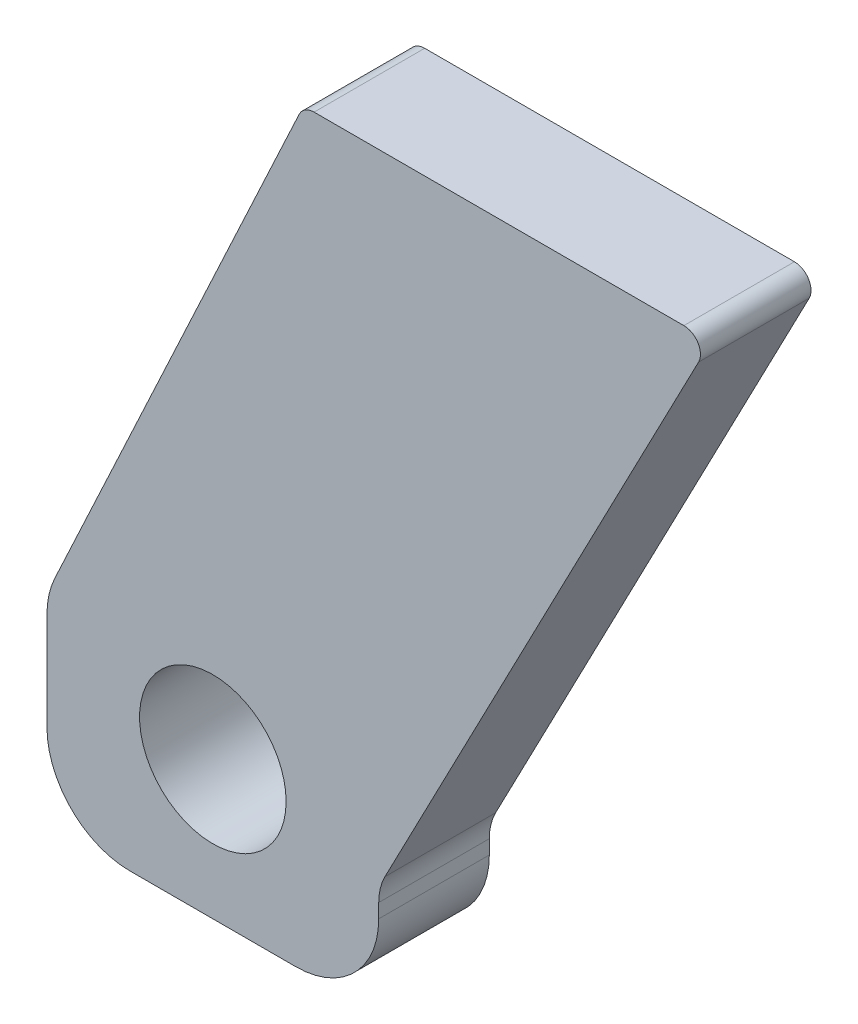
SolidWorks part; units mm, degrees
ref_plane "Plane1" through (0, 0, 0) normal (0, 0, 1) x (1, 0, 0)
ref_plane "Plane2" through (0, 0, 0) normal (0, 1, 0) x (1, 0, 0)
ref_plane "Plane3" through (0, 0, 0) normal (1, 0, 0) x (0, 0, -1)
sketch "Sketch1" plane through (0, 0, 0) normal (0, 0, 1) x (1, 0, 0)
  line L0 (13.25, 0) -> (-30, 0) construction
  line L1 (30, -7.447) -> (30, -10)
  line L3 (18.3088, 110.5) -> (85.1816, 110.5)
  line L4 (0, 0) -> (-65, 0) construction
  line L6 (-30, 7.6746) -> (-30, -10)
  line L7 (-28.5946, 14.0139) -> (15.5899, 108.7679)
  line L9 (0, 0) -> (0, -25) construction
  line L11 (15, -25) -> (-15, -25)
  line L16 (31.1299, -2.8295) -> (87.8427, 106.1148)
  circle A0 centre (0, 0) radius 13.25
  arc A1 (15, -25) -> (30, -10) centre (15, -10) ccw
  arc A2 (-15, -25) -> (-30, -10) centre (-15, -10) cw
  arc A3 (-28.5946, 14.0139) -> (-30, 7.6746) centre (-15, 7.6746) ccw
  arc A4 (31.1299, -2.8295) -> (30, -7.447) centre (40, -7.447) ccw
  arc A5 (85.1816, 110.5) -> (87.8427, 106.1148) centre (85.1816, 107.5) cw
  arc A6 (15.5899, 108.7679) -> (18.3088, 110.5) centre (18.3088, 107.5) cw
  point P10 (-30, 11)
  point P17 (-30, -25)
  point P20 (30, -5)
  point P38 (-30, 11)
  dimension "D4" = 25
  dimension "D5" = 26.5
  dimension "D8" = 2.5
  dimension "D7" = 60
  dimension "D10" = 15
  dimension "D11" = 15
  dimension "D12" = 15
  dimension "D13" = 10
  dimension "D14" = 3
  dimension "D2" = 110.5
  dimension "D3" = 11
  dimension "D6" = 25
  dimension "D9" = 20
  dimension "D1" = 30
extrude "Base-Extrude" add sketch "Sketch1" along normal blind 20
